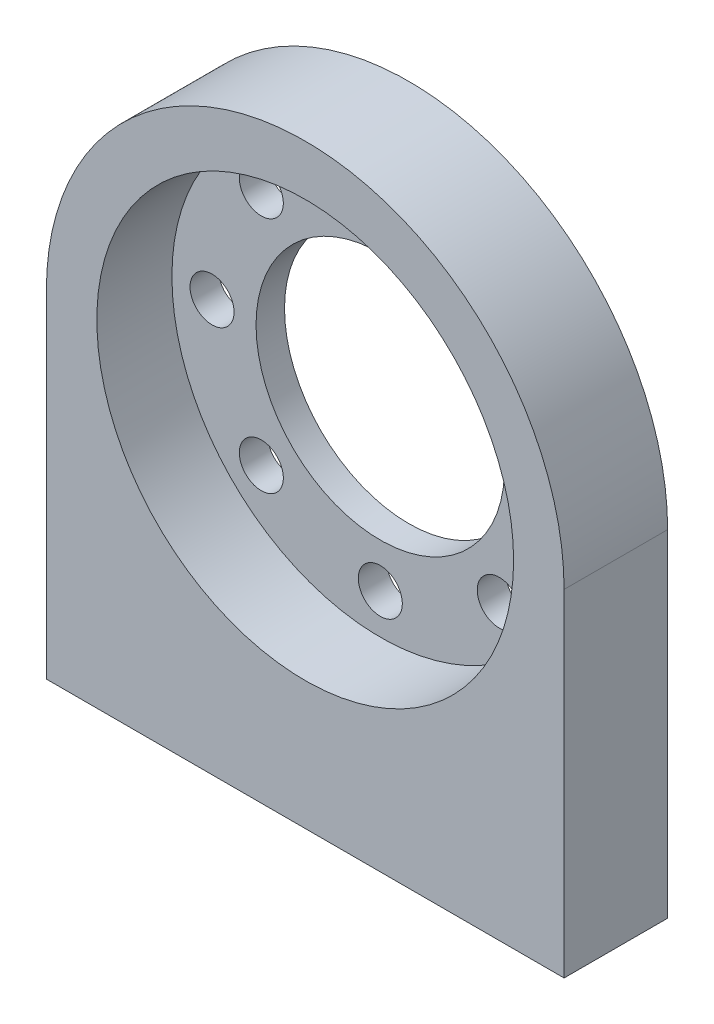
SolidWorks part; units mm, degrees
ref_plane "Plan de face" through (0, 0, 0) normal (0, 0, 1) x (1, 0, 0)
ref_plane "Plan de dessus" through (0, 0, 0) normal (0, 1, 0) x (1, 0, 0)
ref_plane "Plan de droite" through (0, 0, 0) normal (1, 0, 0) x (0, 0, -1)
sketch "Esquisse1" plane through (0, 0, 0) normal (0, 0, 1) x (1, 0, 0)
  line L1 (-20, 0) -> (20, 0) construction
  line L2 (-20, 0) -> (-20, -26)
  line L3 (-20, -26) -> (20, -26)
  line L4 (20, 0) -> (20, -26)
  circle A0 centre (0, 0) radius 20 construction
  arc A1 (-20, 0) -> (20, 0) centre (0, 0) cw
  circle A2 centre (0, 0) radius 9.6
  dimension "D1" = 40
  dimension "D3" = 19.2
  dimension "D2" = 26
extrude "Boss.-Extru.1" add sketch "Esquisse1" along normal blind 8
sketch "Esquisse2" plane through (0, 0, 8) normal (0, 0, 1) x (1, 0, 0)
  circle A0 centre (0, 0) radius 16.1
  dimension "D1" = 32.2
extrude "Enlèv. mat.-Extru.1" cut sketch "Esquisse2" against normal offset from surface (5.8 mm away) 2.2 up to face at (0, -8, 0)
sketch "Esquisse3" plane through (0, 0, 0) normal (0, 0, -1) x (-1, 0, 0)
  line L0 (0, 13) -> (0, 0) construction
  circle A0 centre (0, 13) radius 1.7
  circle A1 centre (9.1924, 9.1924) radius 1.7
  circle A2 centre (13, 0) radius 1.7
  circle A3 centre (9.1924, -9.1924) radius 1.7
  circle A4 centre (0, -13) radius 1.7
  circle A5 centre (-9.1924, -9.1924) radius 1.7
  circle A6 centre (-13, 0) radius 1.7
  circle A7 centre (-9.1924, 9.1924) radius 1.7
  point P17 (0, 0)
  dimension "D1" = 3.4
  dimension "D2" = 13
  dimension "D3" = 8
extrude "Enlèv. mat.-Extru.2" cut sketch "Esquisse3" against normal up to next
sketch "Esquisse4" plane through (0, -26, 0) normal (0, -1, 0) x (1, 0, 0)
  line L0 (0, 0) -> (0, 8) construction
  line L1 (-20, 0) -> (20, 0) construction
  line L2 (-20, 8) -> (20, 8) construction
  line L3 (-16, 4) -> (16, 4) construction
  line L4 (-20, 8) -> (-20, 0) construction
  circle A0 centre (-16, 4) radius 1.25
  circle A1 centre (16, 4) radius 1.25
  point P9 (0, 4)
  dimension "D2" = 2.5
  dimension "D1" = 4
extrude "Enlèv. mat.-Extru.3" cut sketch "Esquisse4" against normal blind 15
